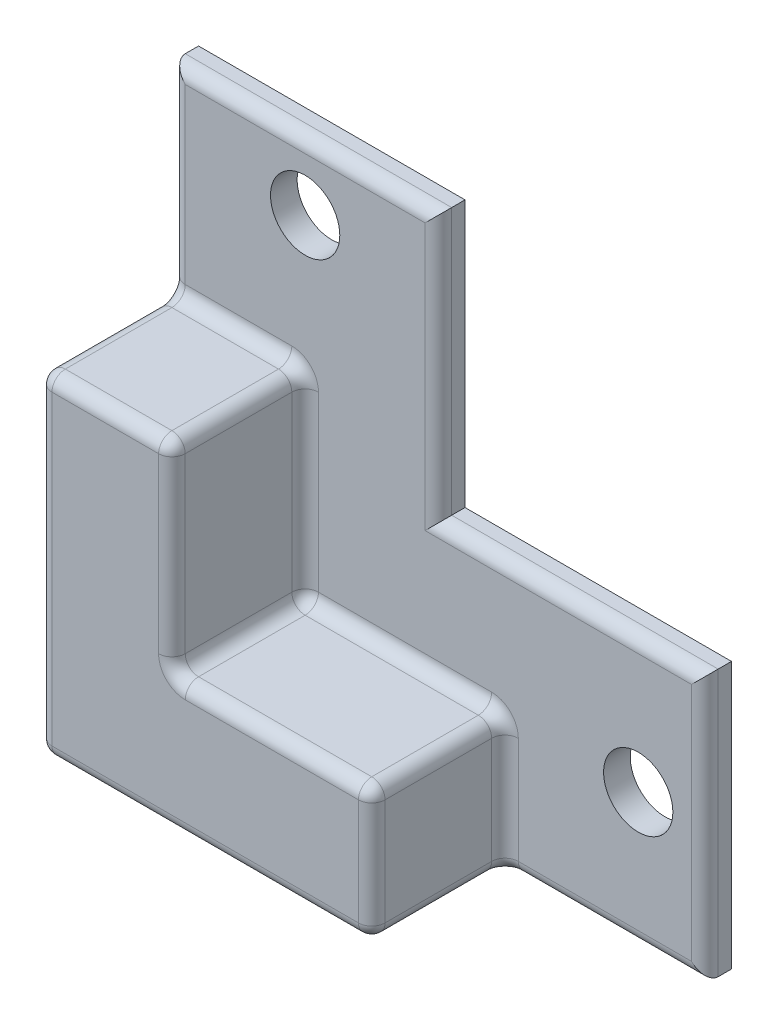
SolidWorks part; units mm, degrees
ref_plane "Front Plane" through (0, 0, 0) normal (0, 0, 1) x (1, 0, 0)
ref_plane "Top Plane" through (0, 0, 0) normal (0, 1, 0) x (1, 0, 0)
ref_plane "Right Plane" through (0, 0, 0) normal (1, 0, 0) x (0, 0, -1)
sketch "Sketch1" plane through (0, 0, 0) normal (0, 0, 1) x (1, 0, 0)
  line L0 (0, 20) -> (0, 0)
  line L1 (-20, -20) -> (20, -20)
  line L2 (-20, -20) -> (-20, 20)
  line L3 (-20, 20) -> (20, 20) construction
  line L4 (20, -20) -> (20, 20) construction
  line L5 (-20, -20) -> (20, 20) construction
  line L6 (-20, 20) -> (20, -20) construction
  line L7 (0, 0) -> (20, 0)
  line L8 (0, 20) -> (-20, 20)
  line L9 (20, 0) -> (20, -20)
  line L10 (20, -10) -> (-20, -10) construction
  line L11 (-10, 20) -> (-10, -20) construction
  circle A0 centre (-10, 15) radius 2.6
  circle A1 centre (15, -10) radius 2.6
  point P0 (0, 0)
  dimension "D3" = 5.2
  dimension "D4" = 5.2
  dimension "D6" = 5
  dimension "D1" = 20
  dimension "D2" = 20
  dimension "D5" = 5
extrude "Boss-Extrude1" add sketch "Sketch1" along normal blind 2
sketch "Sketch2" plane through (0, 0, 2) normal (0, 0, 1) x (1, 0, 0)
  line L0 (-10, 20) -> (-10, -20) construction
  line L1 (0, 20) -> (-20, 20) construction
  line L2 (-20, -20) -> (20, -20) construction
  line L3 (20, -10) -> (-20, -10) construction
  line L4 (20, -20) -> (20, 0) construction
  line L5 (-20, 20) -> (-20, -20) construction
  line L6 (-10, 5) -> (-20, 5)
  line L7 (-20, 5) -> (-20, -20)
  line L8 (-20, -20) -> (5, -20)
  line L9 (5, -20) -> (5, -10)
  line L10 (5, -10) -> (-10, -10)
  line L11 (-10, -10) -> (-10, 5)
  dimension "D1" = 25
  dimension "D2" = 25
extrude "Boss-Extrude2" add sketch "Sketch2" along normal blind 10
fillet "Fillet1" radius 1 22 edges at (-20, 12.5, 2) (12.5, -20, 2) (-15, 5, 2) (5, -20, 7) (5, -15, 2) (5, -10, 7) (-2.5, -10, 2) (-10, -10, 7) (-10, 5, 7) (-10, -2.5, 2) (-2.5, -10, 12) (5, -15, 12) (-7.5, -20, 12) (-20, -7.5, 12) (-15, 5, 12) (-10, -2.5, 12) (20, -10, 2) (10, 0, 2) (0, 10, 2) (-10, 20, 2) (-20, -20, 6) (-20, 5, 7)
